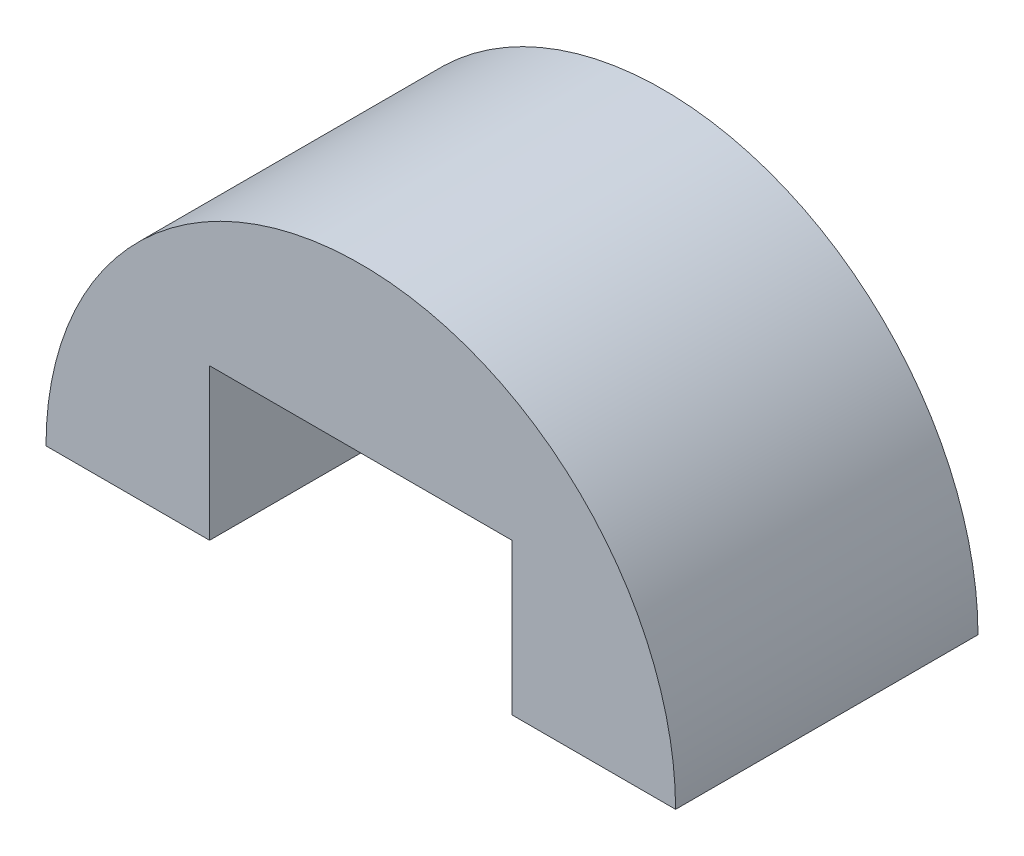
SolidWorks part; units mm, degrees
ref_plane "Front Plane" through (0, 0, 0) normal (0, 0, 1) x (1, 0, 0)
ref_plane "Top Plane" through (0, 0, 0) normal (0, 1, 0) x (1, 0, 0)
ref_plane "Right Plane" through (0, 0, 0) normal (1, 0, 0) x (0, 0, -1)
sketch "Model" plane through (0, 0, 0) normal (0, 0, 1) x (1, 0, 0)
  line L0 (3818.6196, 1740.4722) -> (3821.8652, 1740.4722)
  line L1 (3827.8652, 1740.4722) -> (3831.1109, 1740.4722)
  line L4 (3821.8652, 1740.4722) -> (3821.8652, 1743.4722)
  line L5 (3821.8652, 1743.4722) -> (3827.8652, 1743.4722)
  line L6 (3827.8652, 1743.4722) -> (3827.8652, 1740.4722)
  arc A0 (3831.1109, 1740.4722) -> (3818.6196, 1740.4722) centre (3824.8652, 1740.4722) ccw
extrude "Boss-Extrude1" add sketch "Model" along normal blind 6 contours A0 L0 L4 L5 L6 L1
